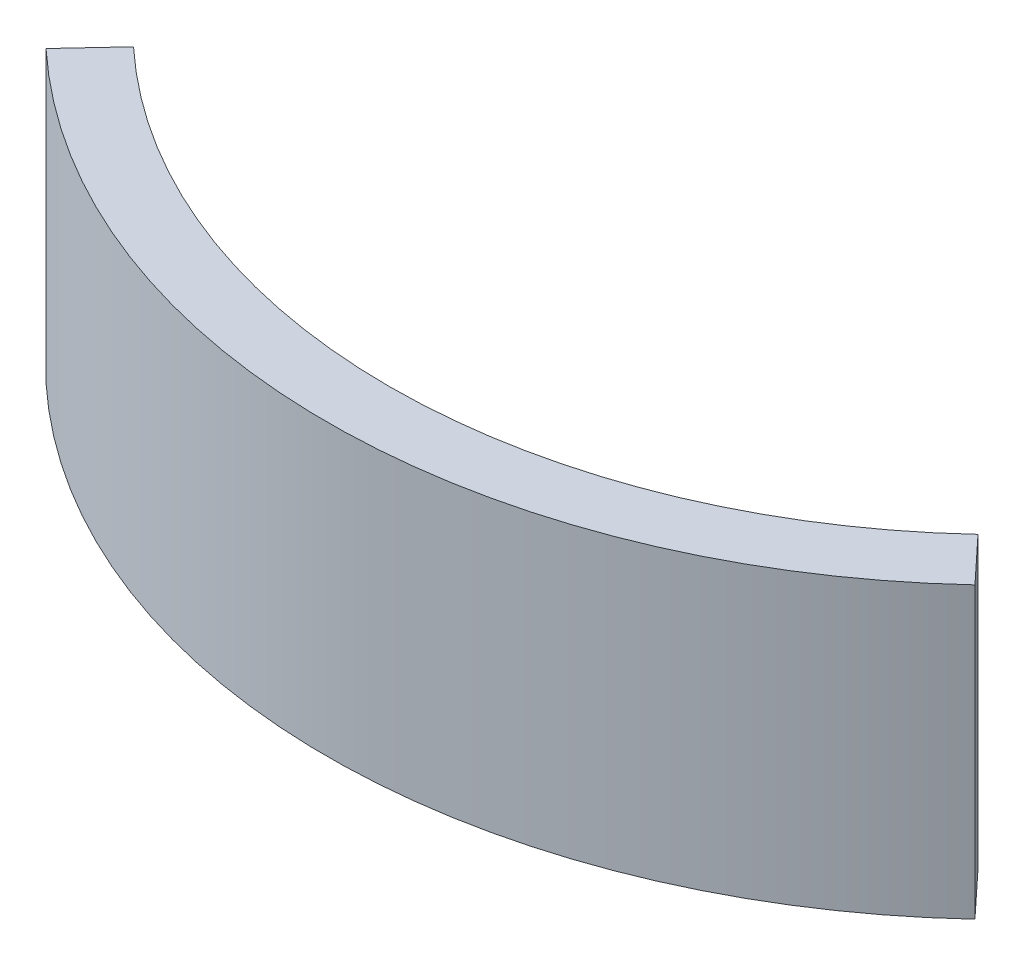
SolidWorks part; units mm, degrees
ref_plane "Front Plane" through (0, 0, 0) normal (0, 0, 1) x (1, 0, 0)
ref_plane "Top Plane" through (0, 0, 0) normal (0, 1, 0) x (1, 0, 0)
ref_plane "Right Plane" through (0, 0, 0) normal (1, 0, 0) x (0, 0, -1)
sketch "Sketch1" plane through (0, 0, 0) normal (0, 1, 0) x (1, 0, 0)
  line L0 (9.7526, 3.8416) -> (8.866, 4.7924)
  line L1 (-8.866, 4.7924) -> (-9.7526, 3.8416)
  arc A0 (-9.7526, 3.8416) -> (9.7526, 3.8416) centre (0, 14.3) ccw
  arc A1 (-8.866, 4.7924) -> (8.866, 4.7924) centre (0, 14.3) ccw
  dimension "D1" = 14.3
  dimension "D2" = 13
  dimension "D3" = 8.866
  dimension "D4" = 3.8416
extrude "Boss-Extrude1" add sketch "Sketch1" along normal blind 6.08
